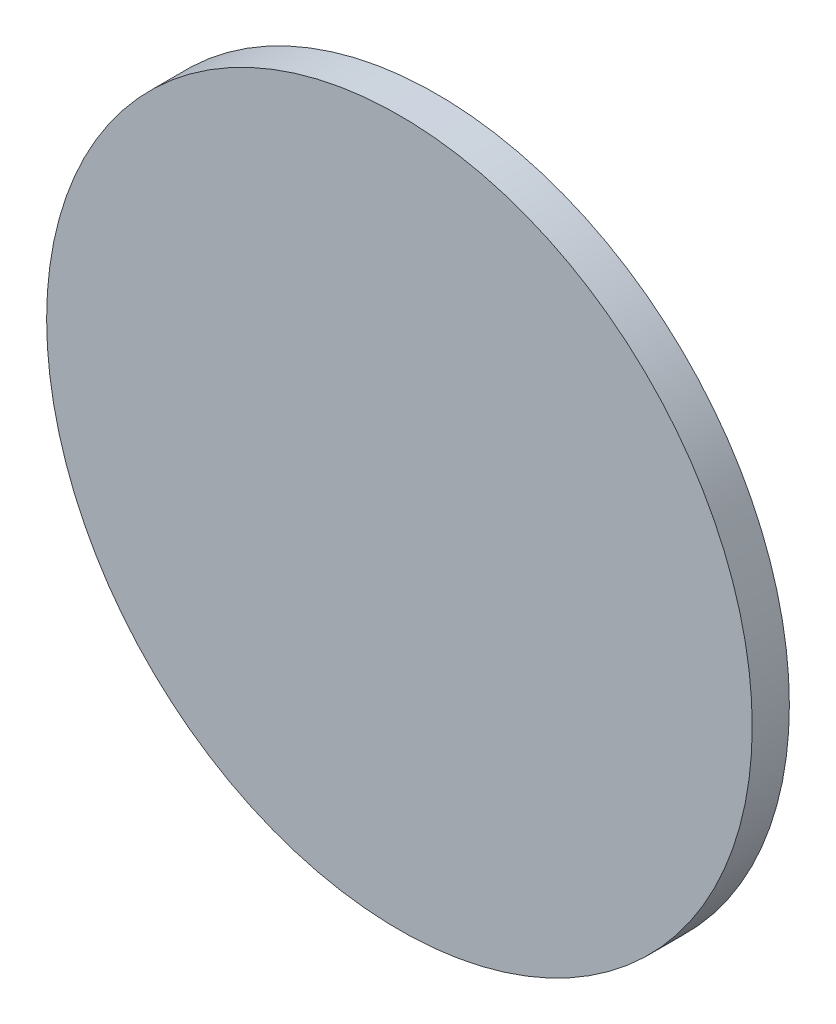
SolidWorks part; units mm, degrees
material "Стекло"
ref_plane "Front" through (0, 0, 0) normal (0, 0, 1) x (1, 0, 0)
ref_plane "Top" through (0, 0, 0) normal (0, 1, 0) x (1, 0, 0)
ref_plane "Right" through (0, 0, 0) normal (1, 0, 0) x (0, 0, -1)
sketch "Эскиз1" plane through (0, 0, 0) normal (0, 0, 1) x (1, 0, 0)
  circle A0 centre (0, 0) radius 19
  dimension "D1" = 38
extrude "Бобышка-Вытянуть1" add sketch "Эскиз1" along normal blind 2
